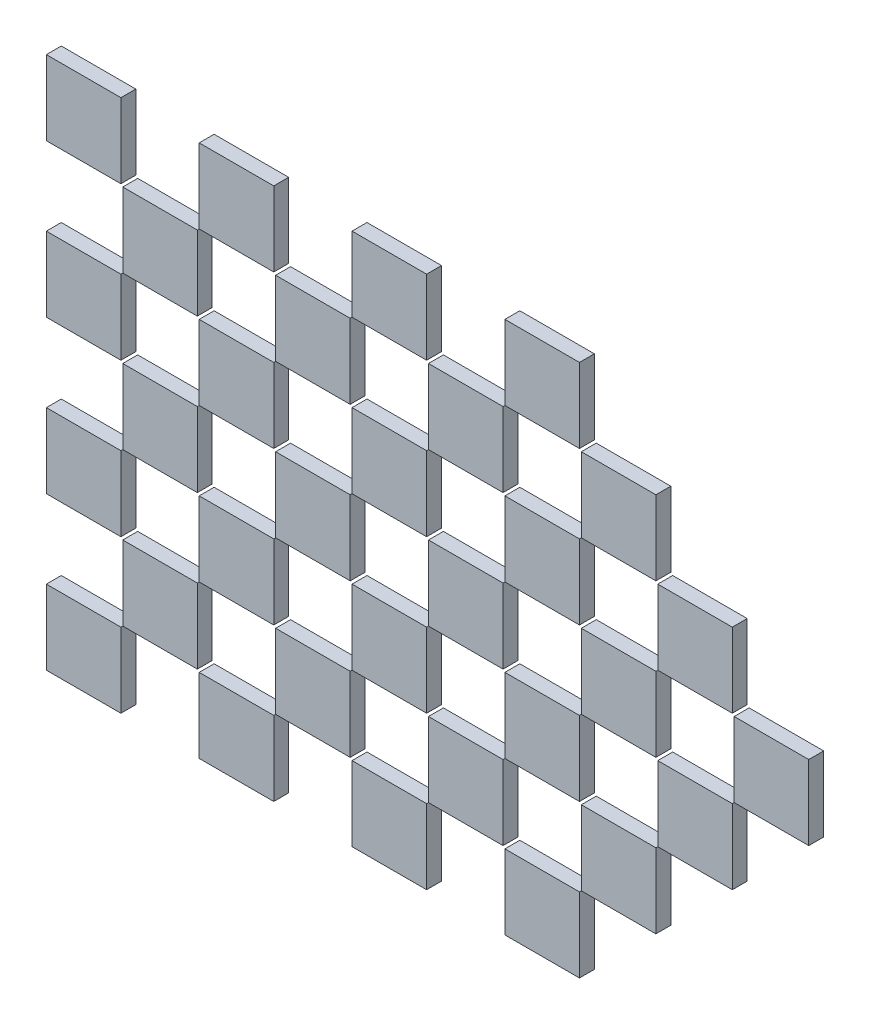
SolidWorks part; units mm, degrees
ref_plane "前视基准面" through (0, 0, 0) normal (0, 0, 1) x (1, 0, 0)
ref_plane "上视基准面" through (0, 0, 0) normal (0, 1, 0) x (1, 0, 0)
ref_plane "右视基准面" through (0, 0, 0) normal (1, 0, 0) x (0, 0, -1)
other "Configuration Table"
sketch "草图1" plane through (0, 0, 0) normal (0, 0, 1) x (1, 0, 0)
  line L1 (-6.7053, 8.1158) -> (-4.7053, 8.1158)
  line L2 (-6.7053, 8.1158) -> (-6.7053, 6.1158)
  line L3 (-6.7053, 6.1158) -> (-4.7053, 6.1158)
  line L4 (-4.7053, 8.1158) -> (-4.7053, 6.1158)
  dimension "D1" = 2
  dimension "D2" = 2
extrude "凸台-拉伸1" add sketch "草图1" along normal blind 0.4
pattern_linear "阵列(线性)1" count 4 spacing 4.1 along (0, 1, 0) count 6 spacing 4.1 along (1, 0, 0) of "凸台-拉伸1"
sketch "草图2" plane through (0, 0, 0) normal (0, 0, 1) x (1, 0, 0)
  line L5 (-4.7053, 10.2158) -> (-2.6053, 8.1158) construction
  line L6 (-2.6053, 10.2158) -> (-4.7053, 8.1158) construction
  line L7 (-4.6553, 8.1658) -> (-2.6553, 8.1658)
  line L8 (-4.6553, 8.1658) -> (-4.6553, 10.1658)
  line L9 (-4.6553, 10.1658) -> (-2.6553, 10.1658)
  line L10 (-2.6553, 8.1658) -> (-2.6553, 10.1658)
  line L11 (-4.6553, 8.1658) -> (-2.6553, 10.1658) construction
  line L12 (-4.6553, 10.1658) -> (-2.6553, 8.1658) construction
  point P0 (-3.6553, 9.1658)
  dimension "D1" = 2
extrude "凸台-拉伸2" add sketch "草图2" along normal blind 0.4 separate body
pattern_linear "阵列(线性)2" count 3 spacing 4.1 along (0, 1, 0) count 5 spacing 4.1 along (1, 0, 0) of "凸台-拉伸2"
delete or keep bodies "实体-删除/保留 1" type delete bodies bodies 126 129 128 127 125 190 170 122
